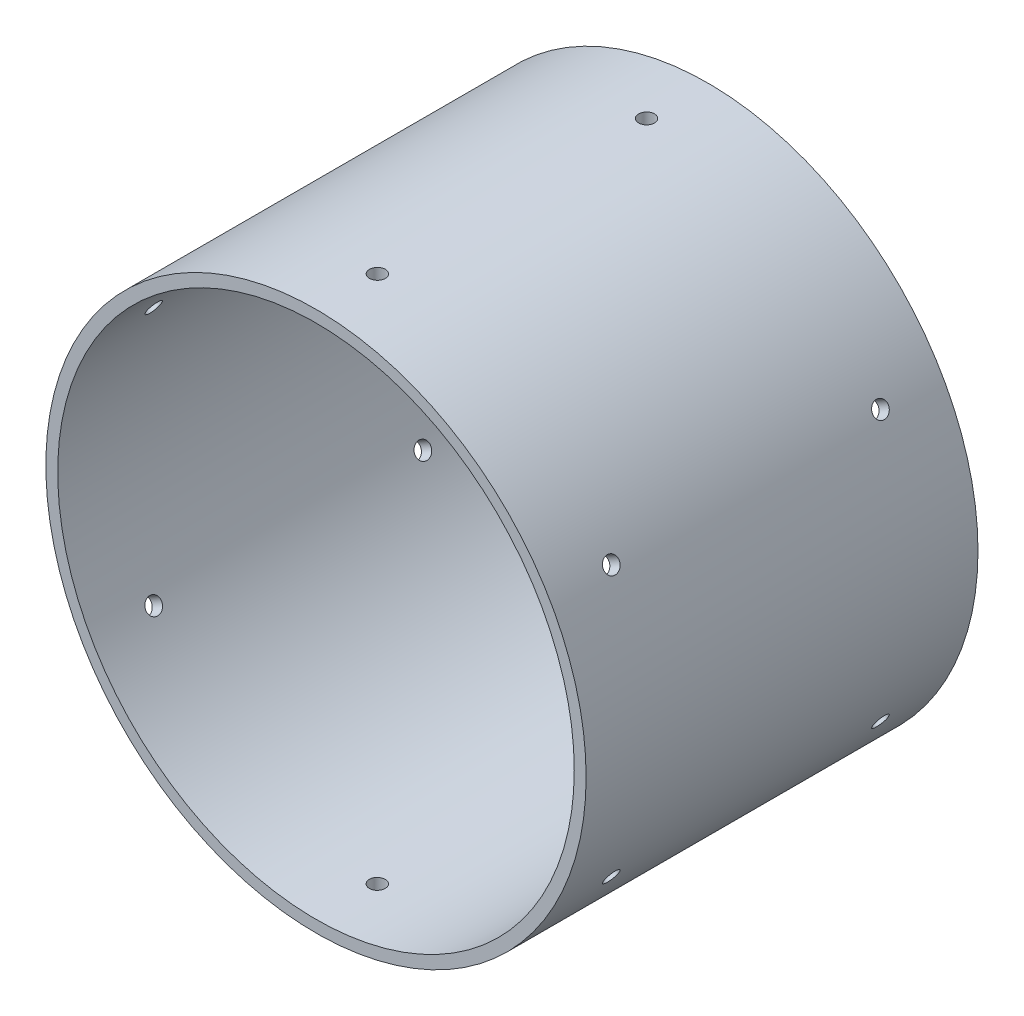
SolidWorks part; units mm, degrees
ref_plane "Front Plane" through (0, 0, 0) normal (0, 0, 1) x (1, 0, 0)
ref_plane "Top Plane" through (0, 0, 0) normal (0, 1, 0) x (1, 0, 0)
ref_plane "Right Plane" through (0, 0, 0) normal (1, 0, 0) x (0, 0, -1)
sketch "Sketch1" plane through (0, 0, 0) normal (0, 0, 1) x (1, 0, 0)
  circle A1 centre (0, 0) radius 68.25
  circle A2 centre (0, 0) radius 65.25
  circle A3 centre (0, 0) radius 65.25
  dimension "D1" = 0.75
  dimension "D2" = 3
extrude "Boss-Extrude1" add sketch "Sketch1" against normal up to surface (99 mm away)
ref_plane "Plane1" through (41.5345, -28.3101, -87.5) normal (0.866, -0.5, 0) x (0, 0, -1)
sketch "Sketch2" plane through (41.5345, -28.3101, -87.5) normal (0.866, -0.5, 0) x (0, 0, -1)
  circle A0 centre (-4, 3.75) radius 2 construction
  circle A1 centre (-4, 3.75) radius 2
  circle A2 centre (-72, 3.75) radius 2 construction
  circle A3 centre (-72, 3.75) radius 2
extrude "Cut-Extrude1" cut sketch "Sketch2" against normal through all both and the other way through all
ref_plane "Plane2" through (3.75, 50.125, -87.5) normal (0, 1, 0) x (1, 0, 0)
sketch "Sketch3" plane through (3.75, 50.125, -87.5) normal (0, 1, 0) x (1, 0, 0)
  circle A0 centre (-3.75, -4) radius 2 construction
  circle A1 centre (-3.75, -4) radius 2
  circle A2 centre (-3.75, -72) radius 2 construction
  circle A3 centre (-3.75, -72) radius 2
extrude "Cut-Extrude2" cut sketch "Sketch3" against normal through all both and the other way through all
ref_plane "Plane3" through (41.6039, 19.6899, -87.5) normal (0.866, 0.5, 0) x (0, 0, -1)
sketch "Sketch4" plane through (41.6039, 19.6899, -87.5) normal (0.866, 0.5, 0) x (0, 0, -1)
  circle A0 centre (-4, 3.75) radius 2 construction
  circle A1 centre (-4, 3.75) radius 2
  circle A2 centre (-72, 3.75) radius 2 construction
  circle A3 centre (-72, 3.75) radius 2
extrude "Cut-Extrude3" cut sketch "Sketch4" against normal through all both and the other way through all
